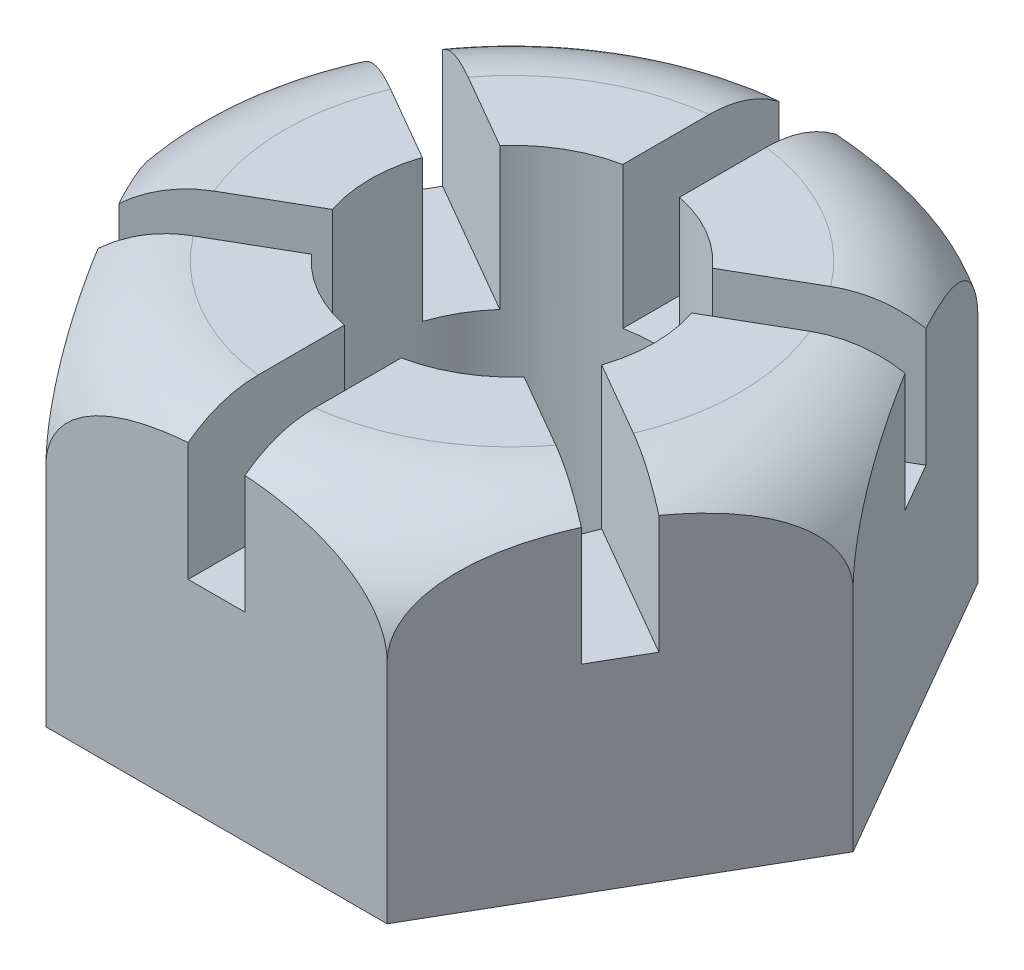
SolidWorks part; units mm, degrees
ref_plane "Front Plane" through (0, 0, 0) normal (0, 0, 1) x (1, 0, 0)
ref_plane "Top Plane" through (0, 0, 0) normal (0, 1, 0) x (1, 0, 0)
ref_plane "Right Plane" through (0, 0, 0) normal (1, 0, 0) x (0, 0, -1)
sketch "Sketch1" plane through (0, 0, 0) normal (0, 1, 0) x (1, 0, 0)
  line L1 (-60.0444, 0) -> (-30.0222, -52)
  line L2 (-30.0222, -52) -> (30.0222, -52)
  line L3 (30.0222, -52) -> (60.0444, 0)
  line L4 (60.0444, 0) -> (30.0222, 52)
  line L5 (30.0222, 52) -> (-30.0222, 52)
  line L6 (-30.0222, 52) -> (-60.0444, 0)
  circle A0 centre (0, 0) radius 52 construction
  dimension "D1" = 104
extrude "Boss-Extrude1" add sketch "Sketch1" along normal blind 60
sketch "Sketch2" plane through (0, 60, 0) normal (0, 1, 0) x (1, 0, 0)
  circle A0 centre (0, 0) radius 25
  dimension "D1" = 50
extrude "Cut-Extrude1" cut sketch "Sketch2" against normal blind 60
sketch "Sketch3" plane through (0, 0, 52) normal (0, 0, 1) x (1, 0, 0)
  line L0 (0, 67.7297) -> (0, -21.3595) construction
  line L1 (-5, 60) -> (-5, 35)
  line L2 (-30.0222, 60) -> (30.0222, 60) construction
  line L3 (-5, 35) -> (5, 35)
  line L4 (5, 35) -> (5, 60)
  line L5 (5, 60) -> (-5, 60)
  dimension "D1" = 25
  dimension "D2" = 10
extrude "Cut-Extrude2" cut sketch "Sketch3" against normal blind 40
pattern_circular "CirPattern1" count 6 over 360 about axis through (0, 0, 0) along (0, 1, 0) of "Cut-Extrude2"
sketch "Sketch4" plane through (0, 0, 0) normal (0, 0, 1) x (1, 0, 0)
  line L0 (47.5333, 60) -> (60.0444, 60) construction
  line L1 (60.0444, 60) -> (60.0444, 0) construction
  line L2 (40.0444, 60) -> (60.0444, 60)
  line L3 (60.0444, 60) -> (60.0444, 40)
  arc A0 (40.0444, 60) -> (60.0444, 40) centre (40.0444, 40) cw
  dimension "D1" = 20
revolve "Cut-Revolve1" cut sketch "Sketch4" angle 360 about axis through (0, 0, 0) along (0, 1, 0)
